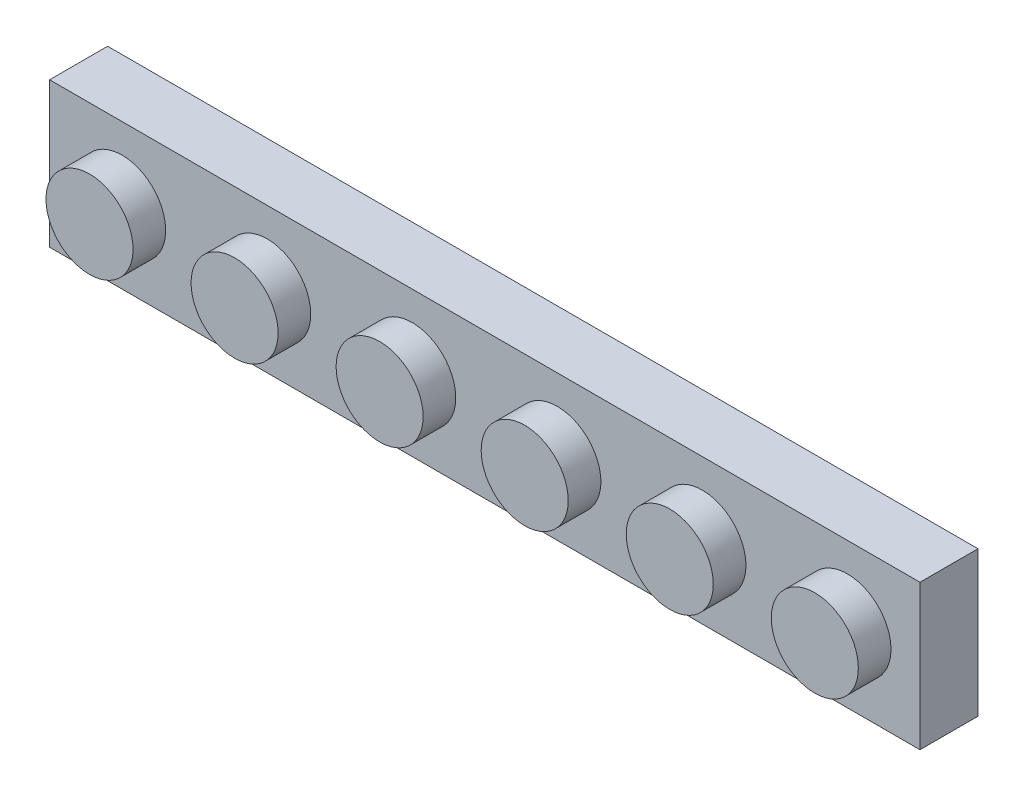
SolidWorks part; units mm, degrees
ref_plane "Front Plane" through (0, 0, 0) normal (0, 0, 1) x (1, 0, 0)
ref_plane "Top Plane" through (0, 0, 0) normal (0, 1, 0) x (1, 0, 0)
ref_plane "Right Plane" through (0, 0, 0) normal (1, 0, 0) x (0, 0, -1)
sketch "Sketch1" plane through (0, 0, 0) normal (0, 0, 1) x (1, 0, 0)
  line L1 (0, 0) -> (48, 0)
  line L2 (0, 0) -> (0, 8)
  line L3 (0, 8) -> (48, 8)
  line L4 (48, 0) -> (48, 8)
  dimension "D1" = 48
  dimension "D2" = 8
extrude "Boss-Extrude1" add sketch "Sketch1" along normal blind 3.2
sketch "Sketch2" plane through (0, 0, 0) normal (0, 0, -1) x (-1, 0, 0)
  line L1 (-46.5, 6.5) -> (-1.5, 6.5)
  line L2 (-46.5, 6.5) -> (-46.5, 1.5)
  line L3 (-46.5, 1.5) -> (-1.5, 1.5)
  line L4 (-1.5, 6.5) -> (-1.5, 1.5)
  dimension "D1" = 45
  dimension "D2" = 5
extrude "Cut-Extrude1" cut sketch "Sketch2" against normal blind 3.1
sketch "Sketch3" plane through (0, 0, 3.2) normal (0, 0, 1) x (1, 0, 0)
  line L0 (0, 8) -> (0, 0) construction
  line L1 (48, 8) -> (0, 8) construction
  circle A0 centre (4, 4) radius 2.4
  dimension "D1" = 4.8
  dimension "D2" = 4
  dimension "D3" = 4
extrude "Boss-Extrude2" add sketch "Sketch3" along normal blind 1.8 contours A0
pattern_linear "LPattern1" count 6 spacing 8 along (1, 0, 0) of "Boss-Extrude2"
sketch "Sketch4" plane through (0, 0, 3.1) normal (0, 0, -1) x (-1, 0, 0)
  line L0 (-46.5, 1.5) -> (-1.5, 1.5) construction
  line L1 (-1.5, 1.5) -> (-1.5, 6.5) construction
  circle A0 centre (-7.95, 3.9) radius 0.8407
  dimension "D2" = 2.4
  dimension "D1" = 6.45
extrude "Boss-Extrude3" add sketch "Sketch4" along normal up to vertex (3.1 mm away) contours A0
pattern_linear "LPattern2" count 5 spacing 8 along (1, 0, 0) of "Boss-Extrude3"
equation "\"$\"= 1.6mm'SwindleClack"
equation "\"D1@Sketch1\"=\"$\" * 5 * 6"
equation "\"D2@Sketch1\"=\"$\" * 5"
equation "\"D1@Boss-Extrude1\"= \"$\" * 2"
equation "\"D1@Sketch2\"=(\"$\" * 5 * 6) - 3mm"
equation "\"D2@Sketch2\"=(\"$\" * 5) - 3mm"
equation "\"D1@Cut-Extrude1\"= (2 * \"$\") - .1mm"
equation "\"D1@Sketch3\"= \"$\" * 3"
equation "\"D2@Sketch3\"= \"$\" *  2.5"
equation "\"D3@Sketch3\"= \"$\" * 2.5"
equation "\"D3@LPattern1\"= \"$\" * 5"
equation "\"D3@LPattern2\"= \"$\" * 5"
